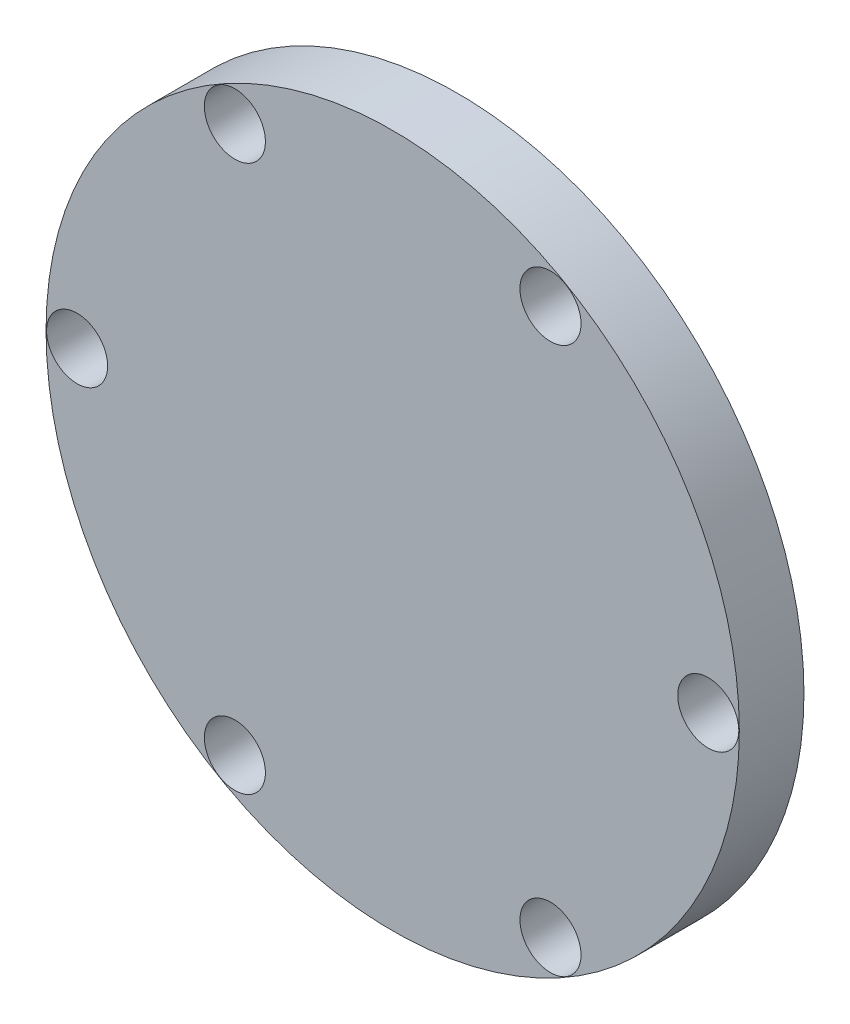
SolidWorks part; units mm, degrees
material "PA Type 6"
ref_plane "Front Plane" through (0, 0, 0) normal (0, 0, 1) x (1, 0, 0)
ref_plane "Top Plane" through (0, 0, 0) normal (0, 1, 0) x (1, 0, 0)
ref_plane "Right Plane" through (0, 0, 0) normal (1, 0, 0) x (0, 0, -1)
sketch "Sketch1" plane through (0, 0, 0) normal (0, 0, 1) x (1, 0, 0)
  circle A0 centre (0, 0) radius 17 construction
  circle A1 centre (-15.5, 0) radius 1.5
  circle A2 centre (-7.75, 13.4234) radius 1.5
  circle A3 centre (7.75, 13.4234) radius 1.5
  circle A4 centre (15.5, 0) radius 1.5
  circle A5 centre (7.75, -13.4234) radius 1.5
  circle A6 centre (-7.75, -13.4234) radius 1.5
  circle A7 centre (0, 0) radius 17.0257
  dimension "D1" = 3
  dimension "D2" = 34
  dimension "D3" = 6
extrude "Boss-Extrude1" add sketch "Sketch1" along normal blind 3.175 contours A0 A6 A5 A4 A3 A2 A1
